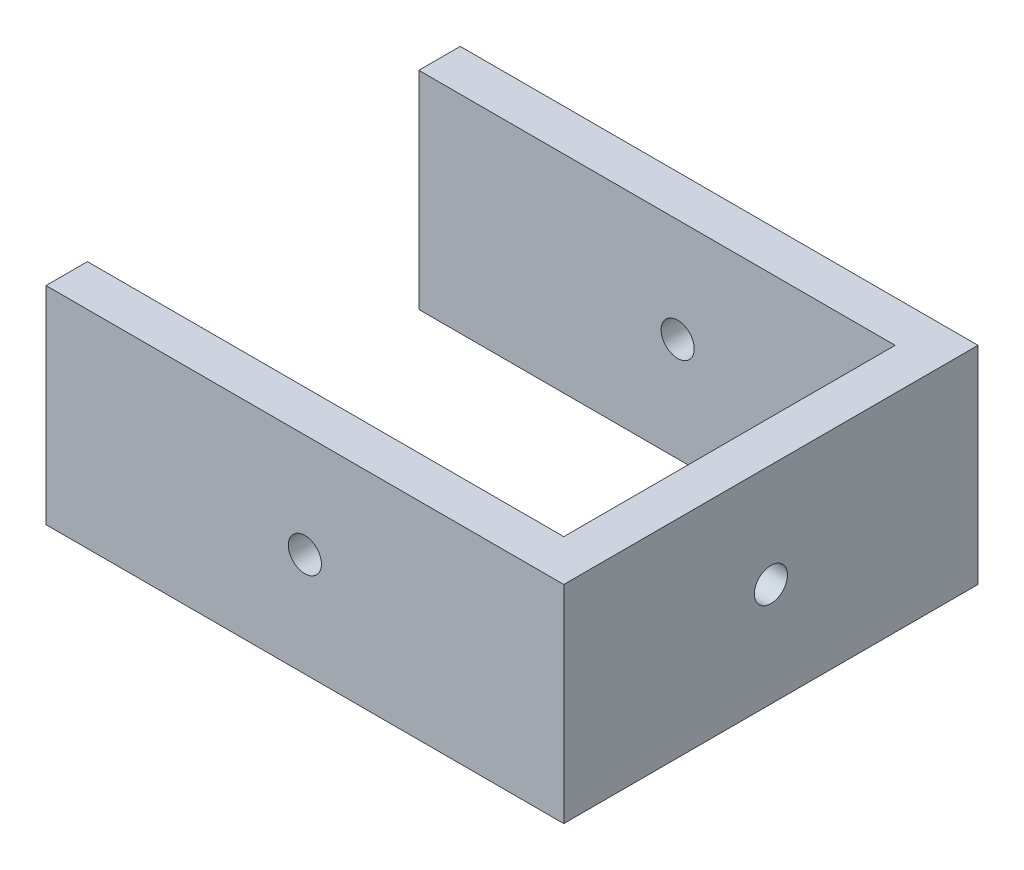
SolidWorks part; units mm, degrees
ref_plane "Front Plane" through (0, 0, 0) normal (0, 0, 1) x (1, 0, 0)
ref_plane "Top Plane" through (0, 0, 0) normal (0, 1, 0) x (1, 0, 0)
ref_plane "Right Plane" through (0, 0, 0) normal (1, 0, 0) x (0, 0, -1)
sketch "Sketch5" plane through (0, 0, 0) normal (1, 0, 0) x (0, 0, -1)
  line L0 (-50, -25) -> (50, 25) construction
  line L1 (-50, 25) -> (50, 25)
  line L2 (-50, 25) -> (-50, -25)
  line L3 (-50, -25) -> (50, -25)
  line L4 (50, 25) -> (50, -25)
  circle A0 centre (0, 0) radius 4
extrude "Boss-Extrude6" add sketch "Sketch5" against normal blind 10
sketch "Sketch6" plane through (0, 0, -50) normal (0, 0, -1) x (-1, 0, 0)
  line L0 (125, -25) -> (0, 25) construction
  line L1 (0, 25) -> (125, 25)
  line L2 (0, 25) -> (0, -25)
  line L3 (0, -25) -> (125, -25)
  line L4 (125, 25) -> (125, -25)
  circle A0 centre (62.5, 0) radius 4
extrude "Boss-Extrude7" add sketch "Sketch6" against normal blind 10
sketch "Sketch7" plane through (0, 0, 50) normal (0, 0, 1) x (1, 0, 0)
  line L0 (-125, -25) -> (-125, 25) construction
  line L1 (0, 25) -> (-125, 25)
  line L2 (0, 25) -> (0, -25)
  line L3 (0, -25) -> (-125, -25)
  line L4 (-125, 25) -> (-125, -25)
  line L5 (0, -25) -> (-125, -25) construction
  line L6 (0, -25) -> (-125, 25) construction
  line L8 (-10, -25) -> (0, -25) construction
  circle A0 centre (-62.5, 0) radius 4
extrude "Boss-Extrude8" add sketch "Sketch7" against normal blind 10
